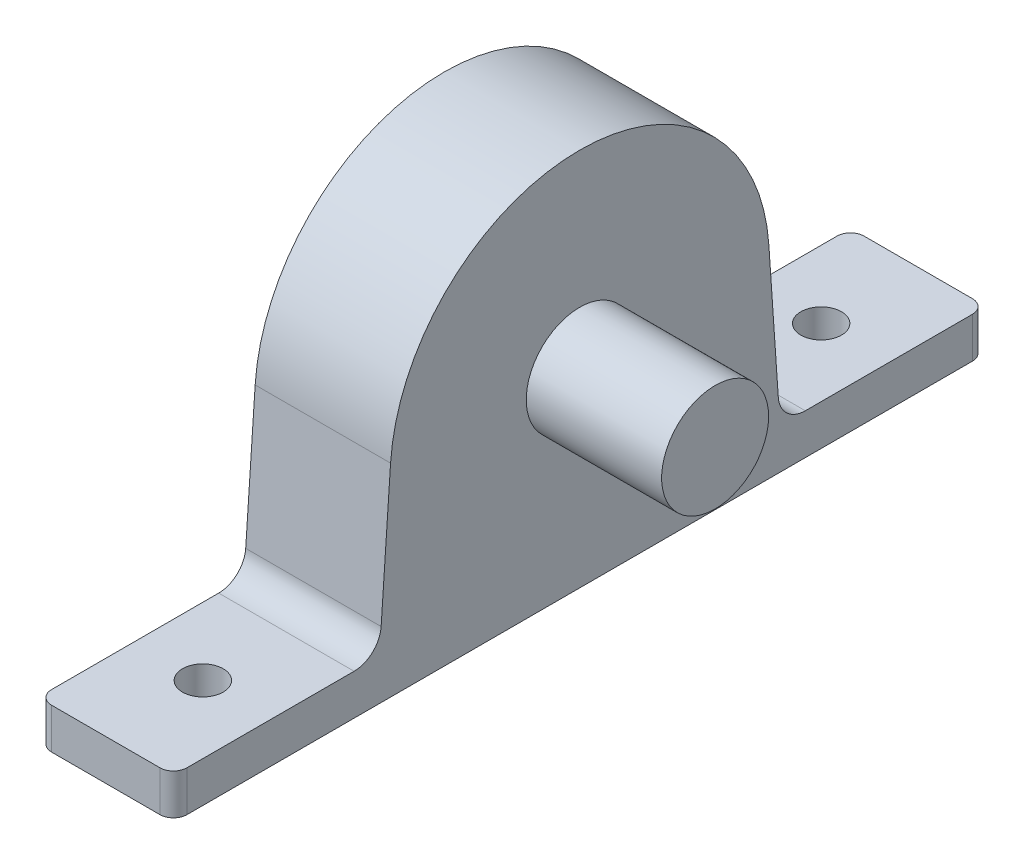
SolidWorks part; units mm, degrees
ref_plane "Front Plane" through (0, 0, 0) normal (0, 0, 1) x (1, 0, 0)
ref_plane "Top Plane" through (0, 0, 0) normal (0, 1, 0) x (1, 0, 0)
ref_plane "Right Plane" through (0, 0, 0) normal (1, 0, 0) x (0, 0, -1)
sketch "Sketch1" plane through (0, 0, 0) normal (1, 0, 0) x (0, 0, -1)
  line L0 (-15, 0) -> (15, 0)
  line L1 (-15, 0) -> (-9.5209, 17.0581)
  line L2 (9.5209, 17.0581) -> (15, 0)
  line L3 (0, 3) -> (-11, 3) construction
  line L4 (0, 25) -> (9.5209, 25) construction
  line L5 (0, 28) -> (15, 28) construction
  line L6 (-15, 0) -> (-13.5737, 20.6565) construction
  line L7 (0, 14) -> (0, 0) construction
  line L8 (15, 0) -> (13.5737, 20.6565) construction
  arc A0 (-9.5209, 17.0581) -> (9.5209, 17.0581) centre (0, 14) cw
  circle A1 centre (0, 14) radius 11 construction
  arc A2 (-12.5173, 7.7296) -> (13.1196, 9.1136) centre (0, 14) ccw construction
  arc A3 (13.9667, 14.9644) -> (-13.9667, 14.9644) centre (0, 14) ccw construction
  point P4 (0, 0)
  point P15 (7.5, 28)
  dimension "D2" = 10
  dimension "D4" = 22
  dimension "D1" = 30
  dimension "D3" = 14
  dimension "D5" = 3
extrude "Boss-Extrude1" add sketch "Sketch1" along normal blind 10
sketch "Sketch2" plane through (10, 0, 0) normal (1, 0, 0) x (0, 0, -1)
  circle A0 centre (0, 14) radius 3.95
  dimension "D1" = 7.9
extrude "Boss-Extrude2" add sketch "Sketch2" along normal blind 10
sketch "Sketch4" plane through (10, 0, 0) normal (1, 0, 0) x (0, 0, -1)
  line L0 (15, 0) -> (13.5737, 20.6565) construction
  line L1 (-15, 0) -> (-13.5737, 20.6565) construction
  line L2 (15, 0) -> (13.5737, 20.6565)
  line L3 (-15, 0) -> (15, 0)
  line L4 (15, 0) -> (9.5209, 17.0581)
  line L5 (-9.5209, 17.0581) -> (-15, 0)
  line L6 (-15, 0) -> (15, 0)
  line L7 (15, 0) -> (9.5209, 17.0581)
  line L8 (-9.5209, 17.0581) -> (-15, 0)
  line L9 (-15, 0) -> (-13.5737, 20.6565)
  arc A0 (13.9667, 14.9644) -> (-13.9667, 14.9644) centre (0, 14) ccw construction
  arc A1 (9.5209, 17.0581) -> (-9.5209, 17.0581) centre (0, 14) ccw
  arc A2 (9.5209, 17.0581) -> (-9.5209, 17.0581) centre (0, 14) ccw
  arc A3 (13.9667, 14.9644) -> (-13.9667, 14.9644) centre (0, 14) ccw
  arc M6 (9.5209, 17.0581) -> (-9.5209, 17.0581) centre (0, 14) ccw
  line M7 (-9.5209, 17.0581) -> (-15, 0)
  line M9 (15, 0) -> (9.5209, 17.0581)
  dimension "D1" = 0
extrude "Boss-Extrude3" add sketch "Sketch4" against normal up to surface (10 mm away) contours L2 A3 L9 M7 M6 M9 up to face at (0, 10.2645, 0)
sketch "Sketch5" plane through (0, 0, 0) normal (0, -1, 0) x (1, 0, 0)
  line L0 (10, 15) -> (10, -15) construction
  line L1 (0, 30) -> (10, 30)
  line L2 (0, 30) -> (0, -30)
  line L3 (0, -30) -> (10, -30)
  line L4 (10, 30) -> (10, -30)
  line L5 (0, 15) -> (0, -15) construction
  point P9 (0, 0)
  dimension "D1" = 60
extrude "Boss-Extrude4" add sketch "Sketch5" against normal blind 3
fillet "Fillet1" radius 1 4 edges at (0, 1.5, -30) (0, 1.5, 30) (10, 1.5, 30) (10, 1.5, -30)
fillet "Fillet2" radius 2 2 edges at (5, 3, -14.7929) (5, 3, 14.7929)
sketch "Sketch7" plane through (0, 3, 0) normal (0, 1, 0) x (1, 0, 0)
  line L0 (1, 30) -> (9, 30) construction
  line L1 (0, -29) -> (0, -16.6595) construction
  line L2 (0, 16.6595) -> (0, 29) construction
  circle A0 centre (5, 22.8298) radius 1.5
  circle A1 centre (5, -22.8298) radius 1.5
  point P6 (5, 30)
  point P9 (0, -22.8298)
  point P12 (0, 22.8298)
  dimension "D1" = 3
extrude "Cut-Extrude1" cut sketch "Sketch7" against normal blind 3
